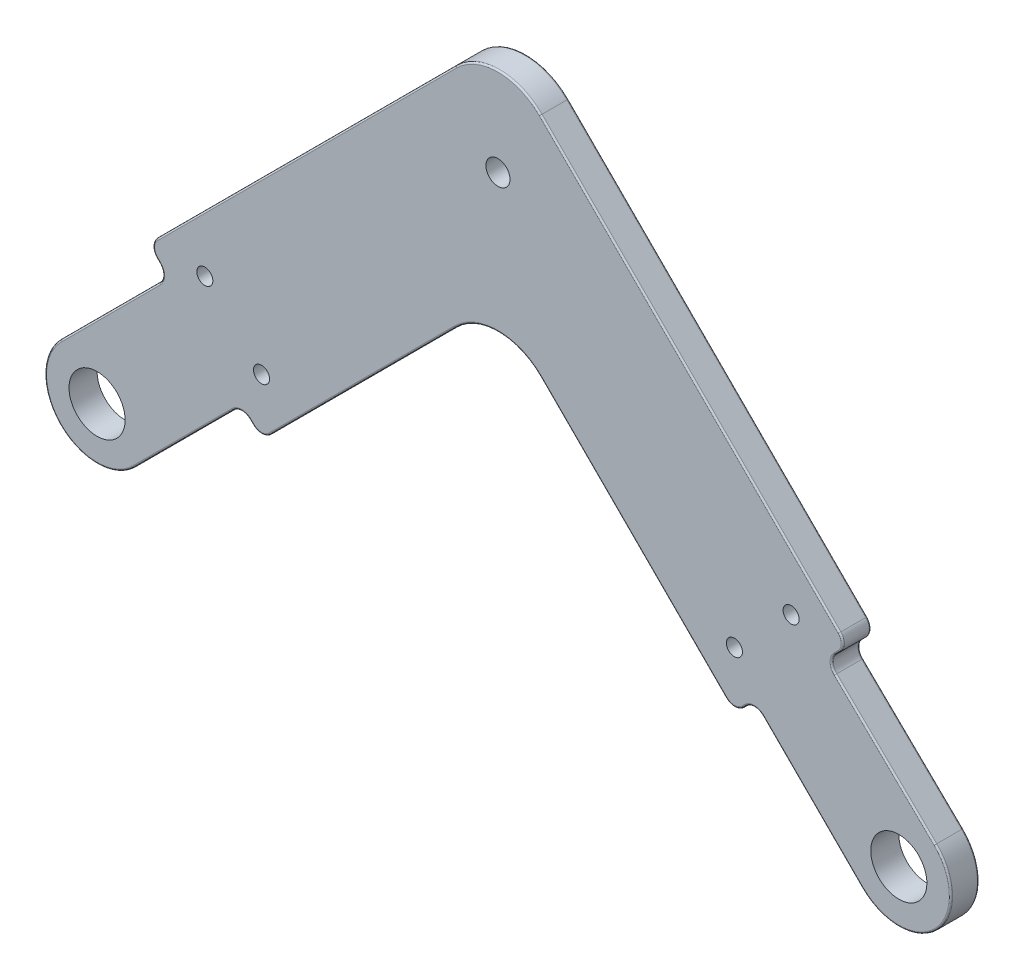
SolidWorks part; units mm, degrees
ref_plane "Front Plane" through (0, 0, 0) normal (0, 0, 1) x (1, 0, 0)
ref_plane "Top Plane" through (0, 0, 0) normal (0, 1, 0) x (1, 0, 0)
ref_plane "Right Plane" through (0, 0, 0) normal (1, 0, 0) x (0, 0, -1)
sketch "Sketch1" plane through (0, 0, 0) normal (0, 0, 1) x (1, 0, 0)
  line L0 (-100, 0) -> (100, 0) construction
  line L1 (-100, 0) -> (0, 100) construction
  line L2 (0, 100) -> (100, 0) construction
  line L3 (0, 0) -> (-50, 50) construction
  line L4 (-40, 60) -> (40, 60) construction
  line L5 (0, 100) -> (0, 60) construction
  circle A0 centre (-100, 0) radius 20
  circle A1 centre (0, 0) radius 20
  circle A2 centre (100, 0) radius 20
  dimension "D5" = 40
  dimension "D1" = 200
  dimension "D2" = 90
  dimension "D3" = 90
  dimension "D4" = 80
sketch "Sketch2" plane through (0, 0, 0) normal (0, 0, 1) x (1, 0, 0)
  line L0 (-56.5165, 43.4835) -> (-40, 60) construction
  line L1 (-100, 0) -> (0, 100) construction
  line L2 (-40, 60) -> (40, 60) construction
  line L3 (40, 60) -> (86.565, 13.435) construction
  line L4 (0, 100) -> (100, 0) construction
  line L5 (-49.4454, 36.4124) -> (-35.8579, 50)
  line L6 (-35.8579, 50) -> (35.8579, 50)
  line L7 (35.8579, 50) -> (79.4939, 6.364)
  line L8 (-63.5876, 50.5546) -> (-44.1421, 70)
  line L9 (-44.1421, 70) -> (44.1421, 70)
  line L10 (44.1421, 70) -> (93.636, 20.5061)
  line L11 (93.636, 20.5061) -> (79.4939, 6.364)
  line L12 (90.9809, 17.8509) -> (104.534, 4.6576)
  line L13 (82.1491, 9.0191) -> (95.3424, -4.534)
  line L14 (90.1005, 24.0416) -> (75.9584, 9.8995) construction
  line L15 (0, 100) -> (0, 60) construction
  line L16 (-6, 70) -> (-3.4532, 85.4203)
  line L17 (6, 70) -> (3.4532, 85.4203)
  line L18 (-63.5876, 50.5546) -> (-49.4454, 36.4124)
  circle A0 centre (100, 0) radius 10
  circle A1 centre (100, 0) radius 3.5
  arc A2 (95.3424, -4.534) -> (104.534, 4.6576) centre (100, 0) ccw
  circle A3 centre (100, 0) radius 20 construction
  circle A4 centre (79.4939, 13.435) radius 1
  circle A5 centre (100, 0) radius 6.5 construction
  circle A6 centre (86.565, 20.5061) radius 1
  circle A7 centre (0, 60) radius 1.5
  circle A8 centre (0, 84.85) radius 1.5
  arc A9 (3.4532, 85.4203) -> (-3.4532, 85.4203) centre (0, 84.85) ccw
  circle A10 centre (-50, 50) radius 1.5
  circle A11 centre (0, 84.85) radius 3.5 construction
  point P29 (106.5, 0)
  point P49 (3.5, 82)
  point P53 (0, 70)
  dimension "D4" = 20
  dimension "D5" = 7
  dimension "D9" = 2
  dimension "D12" = 3
  dimension "D17" = 3
  dimension "D3" = 27.5
  dimension "D7" = 19
  dimension "D8" = 5
  dimension "D10" = 5
  dimension "D11" = 5
  dimension "D13" = 14.85
  dimension "D15" = 6
  dimension "D16" = 6
  dimension "D1" = 10
  dimension "D2" = 10
  dimension "D6" = 3
  dimension "D14" = 2
sketch "Sketch3" plane through (0, 0, 0) normal (0, 0, 1) x (1, 0, 0)
  line L0 (-51.0607, 48.9393) -> (-50, 50)
  line L2 (-50, 50) -> (-48.9393, 48.9393)
  line L4 (-79.4939, 6.364) -> (-50, 35.8579)
  line L5 (-50, 35.8579) -> (-20.5061, 6.364)
  line L6 (-93.636, 20.5061) -> (-50, 64.1421)
  line L7 (-50, 64.1421) -> (-6.364, 20.5061)
  line L8 (-96.0281, 18.114) -> (-50, 64.1421) construction
  line L9 (-81.886, 3.9719) -> (-50, 35.8579) construction
  line L10 (-93.636, 20.5061) -> (-91.1612, 18.0312)
  line L11 (-6.364, 20.5061) -> (-9.0191, 17.8509)
  line L12 (-91.1612, 18.0312) -> (-104.5962, 4.5962)
  line L13 (-81.9688, 8.8388) -> (-95.4038, -4.5962)
  line L14 (-18.0312, 8.8388) -> (-4.5962, -4.5962)
  line L15 (-9.0191, 17.8509) -> (4.534, 4.6576)
  line L16 (-90.0971, 24.045) -> (-75.955, 9.9029) construction
  line L17 (-9.9029, 24.045) -> (-24.045, 9.9029) construction
  line L18 (-81.9688, 8.8388) -> (-79.4939, 6.364)
  line L19 (-18.0312, 8.8388) -> (-20.5061, 6.364)
  line L20 (-88.9571, 11.0429) -> (-50, 50) construction
  line L22 (-50, 50) -> (-13.435, 13.435) construction
  circle A1 centre (-100, 0) radius 3.5
  circle A3 centre (0, 0) radius 3.5
  arc A4 (-4.5962, -4.5962) -> (4.534, 4.6576) centre (0, 0) ccw
  arc A5 (-104.5962, 4.5962) -> (-95.4038, -4.5962) centre (-100, 0) ccw
  circle A6 centre (0, 0) radius 20 construction
  circle A7 centre (-86.5616, 20.5095) radius 1
  circle A8 centre (-79.4905, 13.4384) radius 1
  circle A9 centre (-20.5095, 13.4384) radius 1
  circle A10 centre (-13.4384, 20.5095) radius 1
  circle A11 centre (-50, 50) radius 1.5 construction
  circle A12 centre (-50, 50) radius 1.5
  circle A14 centre (-100, 0) radius 6.5 construction
  circle A15 centre (0, 0) radius 6.5 construction
  point P11 (6.5, 0)
  point P14 (-93.5, 0)
  dimension "D2" = 7
  dimension "D11" = 2
  dimension "D7" = 19
  dimension "D8" = 19
  dimension "D9" = 5
  dimension "D10" = 5
  dimension "D12" = 5
  dimension "D13" = 5
  dimension "D14" = 24.52
  dimension "D15" = 24.52
  dimension "D16" = 24.52
  dimension "D17" = 24.52
  dimension "D3" = 3
  dimension "D4" = 3
  dimension "D5" = 10
  dimension "D6" = 10
sketch "Sketch4" plane through (0, 0, 0) normal (0, 0, 1) x (1, 0, 0)
  line L0 (-57.5, 93.3579) -> (57.5, 93.3579)
  line L1 (57.5, 93.3579) -> (57.5, 83.3579)
  line L2 (57.5, 83.3579) -> (44.1421, 70)
  line L3 (-44.1421, 70) -> (-57.5, 83.3579)
  line L4 (-57.5, 83.3579) -> (-57.5, 93.3579)
  line L5 (-44.1421, 70) -> (44.1421, 70) construction
  line L6 (4, 60) -> (4, 70)
  line L7 (-4, 60) -> (-4, 70)
  line L8 (-22.5, 84.85) -> (22.5, 84.85) construction
  line L9 (-22.5, 89.35) -> (22.5, 89.35)
  line L10 (-22.5, 80.35) -> (22.5, 80.35)
  line L11 (0, 100) -> (0, 60) construction
  circle A0 centre (0, 60) radius 1.5 construction
  circle A1 centre (0, 60) radius 1.5
  circle A2 centre (0, 60) radius 4
  arc A3 (-22.5, 89.35) -> (-22.5, 80.35) centre (-22.5, 84.85) ccw
  arc A4 (22.5, 80.35) -> (22.5, 89.35) centre (22.5, 84.85) ccw
  point P21 (0, 84.85)
  point P36 (0, 93.3579)
  point P39 (0, 80)
  dimension "D6" = 4.5
  dimension "D1" = 115
  dimension "D2" = 10
  dimension "D3" = 10
  dimension "D5" = 45
  dimension "D7" = 4.0079
  dimension "D4" = 2.5
extrude "Boss-Extrude1" add sketch "Sketch3" along normal blind 3.5 contours L12 A5 L13 L18 L4 L5 L19 L14 A4 L15 L11 L7 L6 L10 A12 A10 A9 A8 A7 A1 A3
fillet "Fillet1" radius 7.5 2 edges at (-50, 35.8579, 1.75) (-50, 64.1421, 1.75)
fillet "Fillet2" radius 1.5 8 edges at (-18.0312, 8.8388, 1.75) (-20.5061, 6.364, 1.75) (-6.364, 20.5061, 1.75) (-9.0191, 17.8509, 1.75) (-81.9688, 8.8388, 1.75) (-79.4939, 6.364, 1.75) (-91.1612, 18.0312, 1.75) (-93.636, 20.5061, 1.75)
fillet "Fillet3" radius 0.2 48 edges at (-50, 61.0355, 0) (-73.9393, 40.2028, 0) (-93.0147, 20.5061, 0) (-92.3986, 19.2687, 0) (-91.7825, 18.0312, 0) (-98.409, 10.7834, 0) (-104.5962, -4.5962, 0) (-89.2166, 1.591, 0) (-81.9688, 8.2175, 0) (-80.7313, 7.6014, 0) (-79.4939, 6.9853, 0) (-66.8683, 18.9896, 0) (-50, 32.7513, 0) (-33.1317, 18.9896, 0) (-20.5061, 6.9853, 0) (-19.2687, 7.6014, 0) (-18.0312, 8.2175, 0) (-10.7834, 1.591, 0) (4.627, -4.5652, 0) (-1.6979, 10.724, 0) (-8.3834, 17.8552, 0) (-7.6844, 19.1857, 0) (-6.9853, 20.5061, 0) (-79.4939, 6.9853, 3.5) (-80.7313, 7.6014, 3.5) (-81.9688, 8.2175, 3.5) (-89.2166, 1.591, 3.5) (-104.5962, -4.5962, 3.5) (-98.409, 10.7834, 3.5) (-91.7825, 18.0312, 3.5) (-92.3986, 19.2687, 3.5) (-93.0147, 20.5061, 3.5) (-73.9393, 40.2028, 3.5) (-50, 61.0355, 3.5) (-26.0607, 40.2028, 3.5) (-6.9853, 20.5061, 3.5) (-7.6844, 19.1857, 3.5) (-8.3834, 17.8552, 3.5) (-1.6979, 10.724, 3.5) (4.627, -4.5652, 3.5) (-10.7834, 1.591, 3.5) (-18.0312, 8.2175, 3.5) (-19.2687, 7.6014, 3.5) (-20.5061, 6.9853, 3.5) (-33.1317, 18.9896, 3.5) (-50, 32.7513, 3.5) (-26.0607, 40.2028, 0) (-66.8683, 18.9896, 3.5)
